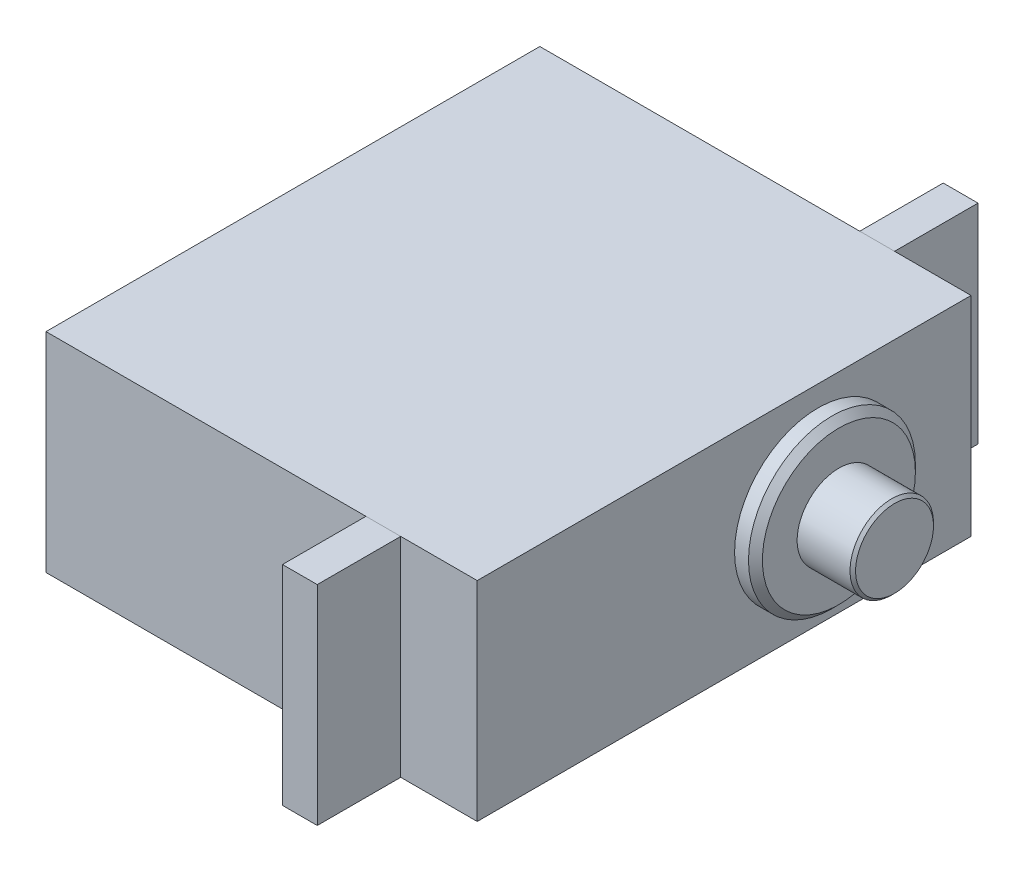
SolidWorks part; units mm, degrees
ref_plane "前视基准面" through (0, 0, 0) normal (0, 0, 1) x (1, 0, 0)
ref_plane "上视基准面" through (0, 0, 0) normal (0, 1, 0) x (1, 0, 0)
ref_plane "右视基准面" through (0, 0, 0) normal (1, 0, 0) x (0, 0, -1)
sketch "草图2" plane through (0, 0, 0) normal (1, 0, 0) x (0, 0, -1)
  line L1 (-17.75, -7.5) -> (17.75, -7.5)
  line L2 (-17.75, -7.5) -> (-17.75, 7.5)
  line L3 (-17.75, 7.5) -> (17.75, 7.5)
  line L4 (17.75, -7.5) -> (17.75, 7.5)
  line L5 (-17.75, -7.5) -> (17.75, 7.5) construction
  line L6 (-17.75, 7.5) -> (17.75, -7.5) construction
  point P0 (0, 0)
  dimension "D1" = 35.5
  dimension "D2" = 15
extrude "凸台-拉伸1" add sketch "草图2" along normal blind 31
sketch "草图3" plane through (0, 7.5, 0) normal (0, 1, 0) x (1, 0, 0)
  line L0 (31, 17.75) -> (0, 17.75) construction
  line L1 (25.5, 17.75) -> (23, 17.75)
  line L2 (25.5, 17.75) -> (25.5, 23.75)
  line L3 (25.5, 23.75) -> (23, 23.75)
  line L4 (23, 17.75) -> (23, 23.75)
  line L5 (31, -17.75) -> (0, -17.75) construction
  line L6 (25.5, -17.75) -> (23, -17.75)
  line L7 (25.5, -17.75) -> (25.5, -23.75)
  line L8 (25.5, -23.75) -> (23, -23.75)
  line L9 (23, -17.75) -> (23, -23.75)
  line L10 (31, 17.75) -> (31, -17.75) construction
  dimension "D1" = 6
  dimension "D2" = 6
  dimension "D3" = 8
  dimension "D4" = 8
  dimension "D5" = 2.5
  dimension "D6" = 2.5
extrude "凸台-拉伸2" add sketch "草图3" against normal blind 15 separate body
sketch "草图4" plane through (31, 0, 0) normal (1, 0, 0) x (0, 0, -1)
  line L0 (17.75, -7.5) -> (17.75, 7.5) construction
  circle A0 centre (6.75, 0) radius 6
  point P2 (17.75, 0)
  dimension "D1" = 12
  dimension "D2" = 11
extrude "凸台-拉伸3" add sketch "草图4" along normal blind 1.5
chamfer "倒角1" distance 0.5 angle 45 1 edges at (32.5, 0, -12.75)
sketch "草图5" plane through (32.5, 0, 0) normal (1, 0, 0) x (0, 0, -1)
  circle A0 centre (6.75, 0) radius 3
  dimension "D1" = 6
extrude "凸台-拉伸4" add sketch "草图5" along normal blind 4
chamfer "倒角2" distance 0.2 angle 45 1 edges at (36.5, 0, -9.75)
